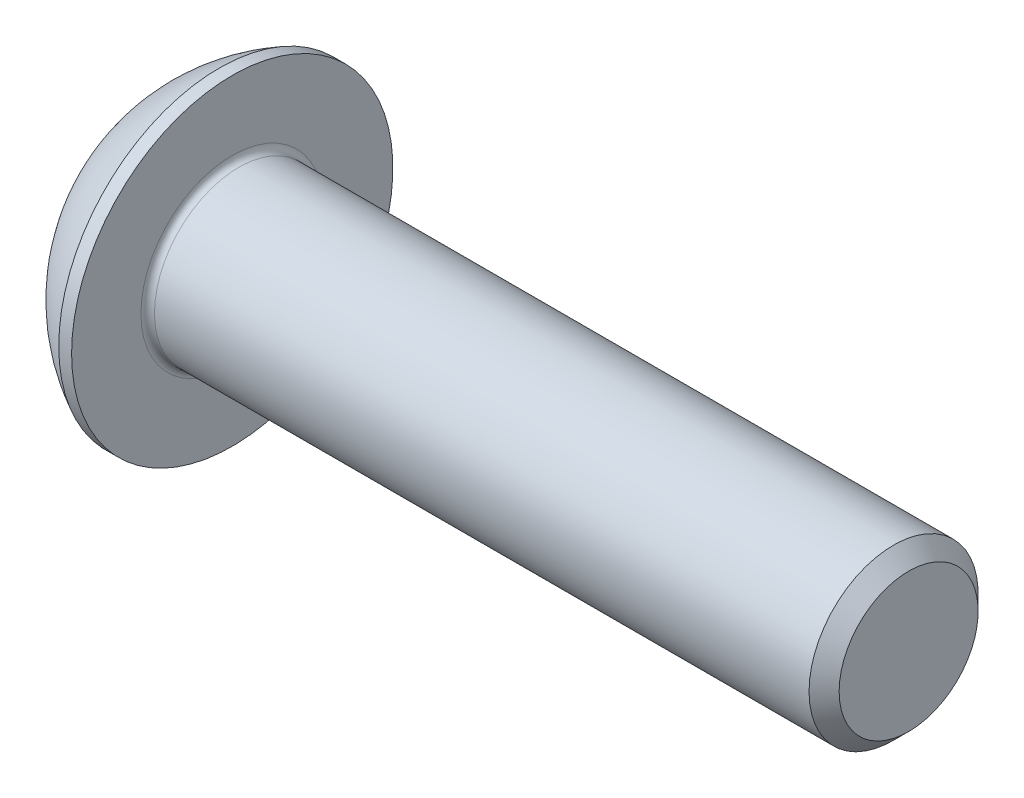
SolidWorks part; units mm, degrees
ref_plane "Plane1" through (0, 0, 0) normal (0, 0, 1) x (1, 0, 0)
ref_plane "Plane2" through (0, 0, 0) normal (0, 1, 0) x (1, 0, 0)
ref_plane "Plane3" through (0, 0, 0) normal (1, 0, 0) x (0, 0, -1)
sketch "BodySke" plane through (0, 0, 0) normal (0, 0, 1) x (1, 0, 0)
  line L0 (22.75, 0) -> (22.75, 2.055)
  line L1 (22.305, 2.5) -> (2.75, 2.5)
  line L2 (2.75, 2.5) -> (2.75, 4.75)
  line L3 (2.75, 4.75) -> (2.37, 4.75)
  line L4 (0, 0) -> (101.6, 0) construction
  line L5 (2.75, -4.75) -> (2.37, -4.75) construction
  line L6 (55.6768, -2.5) -> (2.75, -2.5) construction
  line L7 (22.75, 0) -> (0, 0)
  line L8 (0, 2.375) -> (0, -2.375) construction
  line L9 (0, 0) -> (0, 2.375)
  line L10 (22.75, 2.055) -> (22.305, 2.5)
  line L11 (22.75, -2.055) -> (22.305, -2.5) construction
  line L12 (3.55, 9.525) -> (3.55, -2.5) construction
  line L13 (2.75, 9.525) -> (2.75, -2.5) construction
  arc A1 (0, 2.375) -> (2.37, 4.75) centre (4.755, 0) cw
  dimension "D1" = 4.75
  dimension "Diameter" = 5
  dimension "Length" = 20
  dimension "Head_dia" = 9.5
  dimension "Head_ht" = 2.75
  dimension "Head_side_ht" = 0.38
  dimension "Minor_dia" = 4.11
  dimension "Body_ch_ang" = 45
  dimension "Advance" = 0.8
  dimension "Thread_nom" = 20
revolve "BaseBody" add sketch "BodySke" angle 360 about L4
cosmetic thread "ThreadCosmetic"
fillet "Fillet1" radius 0.2 1 edges at (2.75, 0, 2.5)
sketch "Sketch2" plane through (0, 0, 0) normal (0, 0, 1) x (1, 0, 0)
  line L0 (0, 1.5) -> (1.56, 1.5)
  line L1 (1.56, 1.5) -> (2.426, 0)
  line L3 (2.426, 0) -> (0, 0)
  line L4 (0, 0) -> (0, 1.5)
  line L5 (0, -1.5) -> (1.56, -1.5) construction
  line L6 (0, 0) -> (47.625, 0) construction
  dimension "D2" = 60
  dimension "PreBroach_depth" = 1.56
  dimension "PreBroach_dia" = 3
revolve "PreBroach" cut sketch "Sketch2" angle 360 about L6
sketch "Sketch3" plane through (0, 0, 0) normal (1, 0, 0) x (0, 0, -1)
  line L0 (-1.5, -0.866) -> (-1.5, 0.866)
  line L1 (-1.5, 0.866) -> (0, 1.7321)
  line L2 (0, 1.7321) -> (1.5, 0.866)
  line L3 (1.5, 0.866) -> (1.5, -0.866)
  line L4 (1.5, -0.866) -> (0, -1.7321)
  line L5 (0, -1.7321) -> (-1.5, -0.866)
  dimension "D1" = 1.5
  dimension "D2" = 1.5
  dimension "D3" = 3
  dimension "Hex_size" = 3
extrude "Hex" cut sketch "Sketch3" along normal blind 1.56
sketch "ThdSchSke" plane through (0, 0, 0) normal (0, 0, 1) x (1, 0, 0)
  line L0 (4.35, -2.055) -> (4.0384, -2.5)
  line L1 (4.35, -2.055) -> (4.6616, -2.5)
  line L2 (4.6616, -2.5) -> (4.6616, -3.125)
  line L3 (-3.175, 0) -> (5.1513, 0) construction
  line L5 (4.6616, -3.125) -> (4.0384, -3.125)
  line L6 (4.0384, -3.125) -> (4.0384, -2.5)
  dimension "Thread_minor" = 4.11
  dimension "Diameter" = 5
  dimension "Start" = 4.35
  dimension "SideAngle" = 55
  dimension "VeeAngle" = 70
  dimension "Overcut" = 6.25
revolve "ThreadSchematic" [suppressed] cut sketch "ThdSchSke" angle 360 about L3
pattern_linear "ThdSchPat" [suppressed]
equation "\"D1@BodySke\" = \"Head_dia@BodySke\" * .5"
equation "\"Thread_minor@ThreadCosmetic\" = \"Minor_dia@BodySke\""
equation "\"D1@Sketch3\" = \"Hex_size@Sketch3\" / 2"
equation "\"D2@Sketch3\" = \"D1@Sketch3\""
equation "\"D3@Sketch3\" = \"Hex_size@Sketch3\""
equation "\"Thread_length@ThreadCosmetic\" = ((sgn( (\"Length@BodySke\" - \"Advance@BodySke\" * 2.0) - \"Thread_nom@BodySke\" )-1)*( (\"Length@BodySke\" - \"Advance@BodySke\" * 2.0) - \"Thread_nom@BodySke\" ))/-2+ \"Thread_nom@BodySke\""
equation "\"Thread_minor@ThdSchSke\" = \"Minor_dia@BodySke\""
equation "\"Diameter@ThdSchSke\" = \"Diameter@BodySke\""
equation "\"Overcut@ThdSchSke\" = \"Diameter@BodySke\" * 1.25"
equation "\"Start@ThdSchSke\" = \"Head_ht@BodySke\" + \"Length@BodySke\" - \"Thread_length@ThreadCosmetic\"  '---Non-countersunk---"
equation "\"Num_threads@ThdSchPat\" = int( \"Thread_length@ThreadCosmetic\" / \"Advance@BodySke\" + 0.999 )  + 1"
equation "\"Advance@ThdSchPat\" = \"Thread_length@ThreadCosmetic\" /  (\"Num_threads@ThdSchPat\" - 1) 'relax it"
equation "\"Num_threads@ThdSchPat\" = \"Num_threads@ThdSchPat\" - sgn( \"Num_threads@ThdSchPat\" - 1) '---chamfered tips only---"
